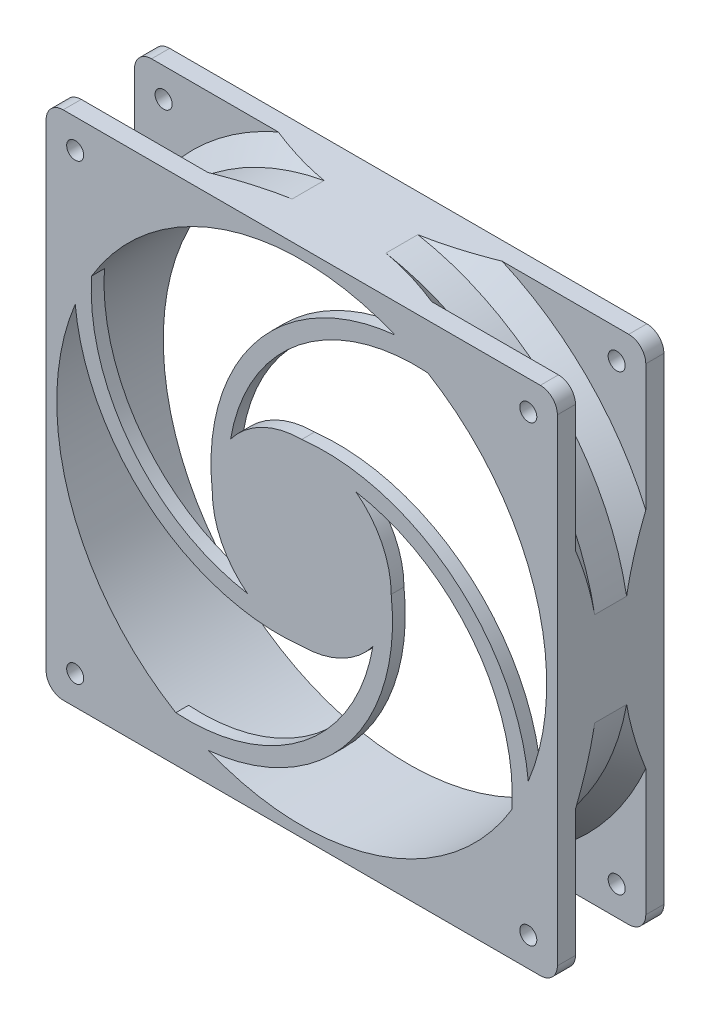
SolidWorks part; units mm, degrees
ref_plane "Front Plane" through (0, 0, 0) normal (0, 0, 1) x (1, 0, 0)
ref_plane "Top Plane" through (0, 0, 0) normal (0, 1, 0) x (1, 0, 0)
ref_plane "Right Plane" through (0, 0, 0) normal (1, 0, 0) x (0, 0, -1)
sketch "Sketch1" plane through (0, 0, 0) normal (0, 0, 1) x (1, 0, 0)
  line L0 (58, -58) -> (58, -30.4344)
  line L1 (60, -60) -> (-60, -60)
  line L2 (60, -60) -> (60, 60)
  line L3 (60, 60) -> (-60, 60)
  line L4 (-60, -60) -> (-60, 60)
  line L5 (60, -60) -> (-60, 60) construction
  line L6 (60, 60) -> (-60, -60) construction
  line L11 (58, 58) -> (30.4344, 58)
  line L12 (-58, -58) -> (-58, -30.4344)
  line L13 (58, -58) -> (30.4344, -58)
  line L14 (-30.4344, 58) -> (-58, 58)
  line L15 (58, 58) -> (-58, 58) construction
  line L16 (58, 30.4344) -> (58, 58)
  line L17 (58, -58) -> (58, 58) construction
  line L18 (-58, 30.4344) -> (-58, 58)
  line L19 (-58, -58) -> (-58, 58) construction
  line L20 (-30.4344, -58) -> (-58, -58)
  line L21 (58, -58) -> (-58, -58) construction
  circle A0 centre (0, 0) radius 57.5
  arc A1 (-30.4344, 58) -> (-58, 30.4344) centre (0, 0) ccw
  arc A2 (58, 30.4344) -> (30.4344, 58) centre (0, 0) ccw
  arc A3 (-58, -30.4344) -> (-30.4344, -58) centre (0, 0) ccw
  arc A4 (30.4344, -58) -> (58, -30.4344) centre (0, 0) ccw
  point P0 (0, 0)
  dimension "D3" = 115
  dimension "D4" = 8
  dimension "D1" = 120
  dimension "D2" = 120
  dimension "D5" = 2
extrude "Boss-Extrude1" add sketch "Sketch1" along normal blind 25 contours A1 L14 L18 | L4 L1 L2 L3 A0 L14 A1 L18 L16 A2 L11 L12 A3 L20 L13 A4 L0 | A4 L13 L0 | A3 L12 L20
fillet "Fillet1" radius 4 4 edges at (60, -60, 12.5) (60, 60, 12.5) (-60, -60, 12.5) (-60, 60, 12.5)
sketch "Sketch2" plane through (0, 0, 0) normal (0, 1, 0) x (1, 0, 0)
  line L0 (61, -8.75) -> (61, -16.25)
  line L2 (61, -16.25) -> (65.5, -20.75)
  line L3 (65.5, -20.75) -> (86, -20.75)
  line L4 (86, -20.75) -> (86, -4.25)
  line L5 (86, -4.25) -> (65.5, -4.25)
  line L6 (65.5, -4.25) -> (61, -8.75)
  line L7 (60, 0) -> (60, -25) construction
  line L8 (0, 0) -> (0, -25) construction
  line L9 (56, 0) -> (-56, 0) construction
  line L10 (56, -25) -> (-56, -25) construction
  point P4 (60, -12.5)
  point P9 (61, -12.5)
  dimension "D1" = 25
  dimension "D2" = 16.5
  dimension "D3" = 4.5
  dimension "D4" = 7.5
  dimension "D5" = 1
revolve "Cut-Revolve1" cut sketch "Sketch2" angle 360 about L8
sketch "Sketch3" plane through (0, 0, 0) normal (0, 0, -1) x (-1, 0, 0)
  line L0 (-58.8284, 58.8284) -> (58.8284, -58.8284) construction
  line L1 (-58.8284, -58.8284) -> (58.8284, 58.8284) construction
  arc A0 (-56, 60) -> (-60, 56) centre (-56, 56) ccw construction
  arc A1 (56, -60) -> (60, -56) centre (56, -56) ccw construction
  arc A2 (-60, -56) -> (-56, -60) centre (-56, -56) ccw construction
  arc A3 (60, 56) -> (56, 60) centre (56, 56) ccw construction
  circle A4 centre (-53.1716, 53.1716) radius 2
  circle A5 centre (53.1716, 53.1716) radius 2
  circle A6 centre (53.1716, -53.1716) radius 2
  circle A7 centre (-53.1716, -53.1716) radius 2
  dimension "D1" = 4
  dimension "D2" = 8
extrude "Cut-Extrude1" cut sketch "Sketch3" against normal through all
sketch "Sketch4" plane through (0, 0, 25) normal (0, 0, 1) x (1, 0, 0)
  arc A0 (0, 21) -> (-16.6912, 12.7438) centre (0, 0) ccw
  arc A1 (-21, 0) -> (21.8868, 53.1716) centre (26.6938, 5.4129) cw
  arc A2 (-16.6912, 12.7438) -> (29.561, 49.3194) centre (26.6938, 5.4129) cw
  arc A3 (-17.0255, 0.4511) -> (22.2874, 49.1917) centre (26.6938, 5.4129) cw construction
  circle A4 centre (0, 0) radius 57.5 construction
  arc A5 (0, 21) -> (53.1716, -21.8868) centre (5.4129, -26.6938) cw
  arc A6 (12.7438, 16.6912) -> (49.3194, -29.561) centre (5.4129, -26.6938) cw
  arc A7 (21, 0) -> (-21.8868, -53.1716) centre (-26.6938, -5.4129) cw
  arc A8 (16.6912, -12.7438) -> (-29.561, -49.3194) centre (-26.6938, -5.4129) cw
  arc A9 (0, -21) -> (-53.1716, 21.8868) centre (-5.4129, 26.6938) cw
  arc A10 (-12.7438, -16.6912) -> (-49.3194, 29.561) centre (-5.4129, 26.6938) cw
  arc A11 (21, 0) -> (12.7438, 16.6912) centre (0, 0) ccw
  arc A12 (0, -21) -> (16.6912, -12.7438) centre (0, 0) ccw
  arc A13 (-49.3194, 29.561) -> (-53.1716, 21.8868) centre (0, 0) ccw
  arc A14 (29.561, 49.3194) -> (21.8868, 53.1716) centre (0, 0) ccw
  arc A15 (49.3194, -29.561) -> (53.1716, -21.8868) centre (0, 0) ccw
  arc A16 (-29.561, -49.3194) -> (-21.8868, -53.1716) centre (0, 0) ccw
  arc A17 (-21, 0) -> (-12.7438, -16.6912) centre (0, 0) ccw
  point P13 (53.1716, 53.1716)
  point P36 (0, 0)
  dimension "D1" = 42
  dimension "D2" = 4
  dimension "D3" = 48
  dimension "D4" = 4
extrude "Boss-Extrude2" add sketch "Sketch4" against normal blind 3
